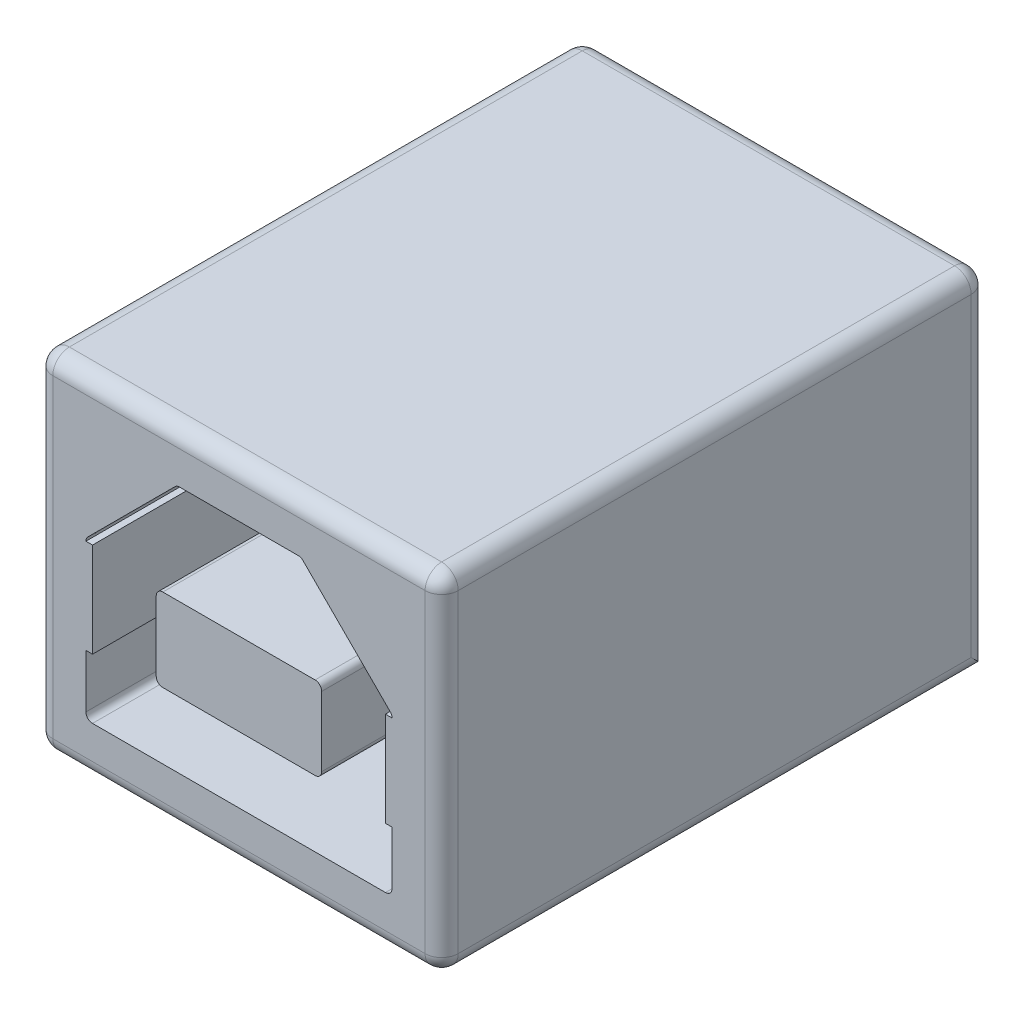
SolidWorks part; units mm, degrees
material "Alloy Steel"
ref_plane "Front Plane" through (0, 0, 0) normal (0, 0, 1) x (1, 0, 0)
ref_plane "Top Plane" through (0, 0, 0) normal (0, 1, 0) x (1, 0, 0)
ref_plane "Right Plane" through (0, 0, 0) normal (1, 0, 0) x (0, 0, -1)
sketch "Sketch1" plane through (0, 0, 0) normal (0, 0, 1) x (1, 0, 0)
  line L1 (0, 0) -> (12.25, 0)
  line L2 (0, 0) -> (0, 10.5)
  line L3 (0, 10.5) -> (12.25, 10.5)
  line L4 (12.25, 0) -> (12.25, 10.5)
  dimension "D1" = 10.5
  dimension "D2" = 12.25
extrude "Boss-Extrude1" add sketch "Sketch1" against normal blind 16.5
sketch "Sketch3" plane through (0, 0, 0) normal (0, 0, 1) x (1, 0, 0)
  line L0 (7.9172, 9) -> (4.3328, 9)
  line L1 (1.5, 6.1672) -> (1.5, 1.7)
  line L2 (1.7, 1.5) -> (10.55, 1.5)
  line L3 (10.75, 1.7) -> (10.75, 6.1672)
  line L4 (0, 10.5) -> (0, 0)
  line L5 (0, 0) -> (12.25, 0)
  line L6 (12.25, 0) -> (12.25, 10.5)
  line L7 (12.25, 10.5) -> (0, 10.5)
  line L8 (0, 10.5) -> (0, 0)
  line L9 (0, 0) -> (12.25, 0)
  line L10 (12.25, 0) -> (12.25, 10.5)
  line L11 (12.25, 10.5) -> (0, 10.5)
  line L12 (10.75, 9) -> (1.5, 9) construction
  line L13 (1.5, 9) -> (1.5, 1.5) construction
  line L14 (4.1914, 8.9414) -> (1.5586, 6.3086)
  line L15 (10.75, 1.5) -> (10.75, 9) construction
  line L16 (10.6914, 6.3086) -> (8.0586, 8.9414)
  line L17 (6.125, 9) -> (6.125, -0.2225) construction
  line L18 (3.825, 6) -> (8.425, 6)
  line L19 (3.625, 5.8) -> (3.625, 3.7)
  line L20 (3.825, 3.5) -> (8.425, 3.5)
  line L21 (8.625, 5.8) -> (8.625, 3.7)
  line L22 (1.5, 1.5) -> (10.75, 1.5) construction
  arc A0 (8.0586, 8.9414) -> (7.9172, 9) centre (7.9172, 8.8) ccw
  arc A1 (4.1914, 8.9414) -> (4.3328, 9) centre (4.3328, 8.8) cw
  arc A2 (1.5586, 6.3086) -> (1.5, 6.1672) centre (1.7, 6.1672) ccw
  arc A3 (10.6914, 6.3086) -> (10.75, 6.1672) centre (10.55, 6.1672) cw
  arc A4 (10.55, 1.5) -> (10.75, 1.7) centre (10.55, 1.7) ccw
  arc A5 (1.5, 1.7) -> (1.7, 1.5) centre (1.7, 1.7) ccw
  arc A6 (3.625, 3.7) -> (3.825, 3.5) centre (3.825, 3.7) ccw
  arc A7 (8.425, 3.5) -> (8.625, 3.7) centre (8.425, 3.7) ccw
  arc A8 (8.425, 6) -> (8.625, 5.8) centre (8.425, 5.8) cw
  arc A9 (3.825, 6) -> (3.625, 5.8) centre (3.825, 5.8) ccw
  point P34 (3.625, 3.5)
  point P37 (8.625, 3.5)
  point P40 (8.625, 6)
  point P43 (3.625, 6)
  dimension "D6" = 0.2
  dimension "D3" = 5
  dimension "D4" = 2.5
  dimension "D5" = 2
  dimension "D1" = 0
  dimension "D2" = 1.5
extrude "Cut-Extrude1" cut sketch "Sketch3" against normal blind 15 contours L1 A5 L2 A4 L3 A3 L16 A0 L0 A1 L14 A2 A9 L18 A8 L21 A7 L20 A6 L19
fillet "Fillet1" radius 0.5 19 edges at (3.6836, 5.9414, -15) (6.125, 6, -15) (8.5664, 5.9414, -15) (8.625, 4.75, -15) (8.5664, 3.5586, -15) (6.125, 3.5, -15) (3.6836, 3.5586, -15) (12.25, 5.25, -16.5) (12.25, 0, -8.25) (12.25, 5.25, 0) (0, 0, -8.25) (0, 5.25, -16.5) (0, 5.25, 0) (0, 10.5, -8.25) (6.125, 10.5, -16.5) (12.25, 10.5, -8.25) (6.125, 10.5, 0) (6.125, 0, 0) (3.625, 4.75, -15)
sketch "Sketch4" plane through (10.75, 0, 0) normal (-1, 0, 0) x (0, 0, 1)
  line L1 (0, 6.1672) -> (-7.0579, 6.1672)
  line L2 (0, 6.1672) -> (0, 3.3108)
  line L3 (0, 3.3108) -> (-7.0579, 3.3108)
  line L4 (-7.0579, 6.1672) -> (-7.0579, 3.3108)
sketch "Sketch8" plane through (1.5, 0, 0) normal (1, 0, 0) x (0, 0, -1)
  line L1 (0, 6.1672) -> (7.0579, 6.1672)
  line L2 (0, 6.1672) -> (0, 3.3108)
  line L3 (0, 3.3108) -> (7.0579, 3.3108)
  line L4 (7.0579, 6.1672) -> (7.0579, 3.3108)
extrude "Boss-Extrude3" add sketch "Sketch8" along normal blind 0.2
extrude "Boss-Extrude4" add sketch "Sketch4" along normal blind 0.2
